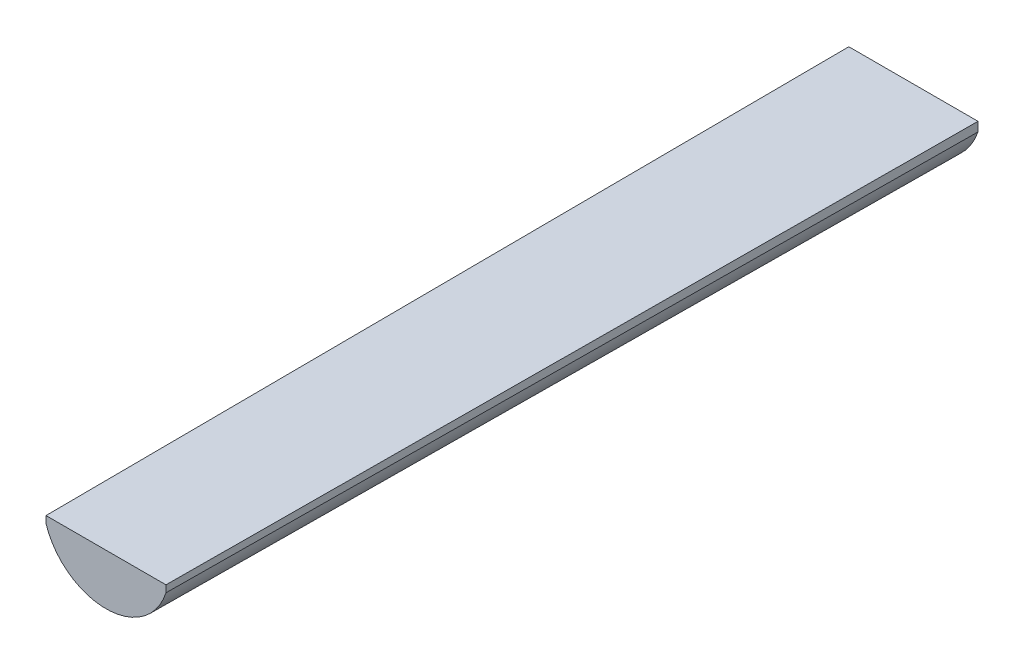
SolidWorks part; units mm, degrees
ref_plane "Přední rovina" through (0, 0, 0) normal (0, 0, 1) x (1, 0, 0)
ref_plane "Horní rovina" through (0, 0, 0) normal (0, 1, 0) x (1, 0, 0)
ref_plane "Pravá rovina" through (0, 0, 0) normal (1, 0, 0) x (0, 0, -1)
sketch "Skica1" plane through (0, 0, 0) normal (1, 0, 0) x (0, 0, -1)
  line L0 (0, 0) -> (350, 0)
  dimension "D1" = 350
sketch "Skica2" plane through (0, 0, 0) normal (0, 0, 1) x (1, 0, 0)
  line L0 (-26, 0) -> (26, 0)
  line L1 (26, 0) -> (26, -3)
  line L2 (-26, 0) -> (-26, -3)
  arc A0 (-26, -3) -> (26, -3) centre (0, 5.2895) ccw
  dimension "D1" = 52
  dimension "D2" = 22
  dimension "D3" = 3
ref_plane "Rovina1" through (0, 0, -350) normal (0, 0, 1) x (1, 0, 0)
sketch "Skica3" plane through (0, 0, -350) normal (0, 0, 1) x (1, 0, 0)
  line L0 (28, 0) -> (-28, 0)
  line L1 (-28, 0) -> (-28, -4)
  line L2 (28, 0) -> (28, -4)
  arc A0 (28, -4) -> (-28, -4) centre (0, 5.6) cw
  dimension "D1" = 56
  dimension "D2" = 4
  dimension "D3" = 24
loft "Spojit profily1" add profiles "Skica2", "Skica3"
sketch "Skica5" plane through (0, 0, 0) normal (0, 1, 0) x (1, 0, 0)
  line L0 (28, 350) -> (-28, 350)
  line L1 (28, 350) -> (27.9429, 340)
  line L2 (26, 0) -> (28, 350) construction
  line L3 (-28, 350) -> (-27.9429, 340)
  line L4 (-26, 0) -> (-28, 350) construction
  arc A0 (27.9429, 340) -> (-27.9429, 340) centre (0, 350.9177) cw
  dimension "D1" = 10
  dimension "D2" = 30
ref_plane "Rovina3" through (0, -100, 0) normal (0, 1, 0) x (1, 0, 0)
sketch "Skica6" plane through (0, -100, 0) normal (0, 1, 0) x (1, 0, 0)
  line L0 (-18, 350) -> (18, 350)
  line L1 (28, 350) -> (-28, 350) construction
  line L2 (-18, 350) -> (-18, 343)
  line L3 (18, 350) -> (18, 343)
  arc A0 (-18, 343) -> (18, 343) centre (0, 343) ccw
  point P2 (0, 350)
  dimension "D3" = 18
  dimension "D1" = 36
  dimension "D2" = 7
ref_plane "Rovina4" through (0, -175, -175) normal (0, -0.7071, -0.7071) x (-1, 0, 0)
sketch "Skica7" plane through (0, -175, -175) normal (0, -0.7071, -0.7071) x (-1, 0, 0)
  line L0 (28, 247.4874) -> (27.7657, 218.4883)
  line L1 (-28, 247.4874) -> (-27.7879, 218.4881)
  line L2 (28, 247.4874) -> (27.9429, 240.4163) construction
  line L3 (-26, -2.1213) -> (-28, 244.6589) construction
  line L4 (-28, 247.4874) -> (28, 247.4874)
  arc A0 (27.7657, 218.4883) -> (-27.7879, 218.4881) centre (-0.0111, 222.0168) cw
  dimension "D1" = 29
  dimension "D2" = 28
ref_plane "Rovina5" through (0, 0, -255) normal (0, 0, -1) x (-1, 0, 0)
sketch "Skica8" plane through (0, 0, -255) normal (0, 0, -1) x (-1, 0, 0)
  line L0 (-27.4571, 0) -> (-27.4571, -0.5)
  line L2 (27.4571, 0) -> (27.4571, -0.5)
  line L4 (-27.4571, 0) -> (27.4571, 0)
  arc A0 (-27.4571, -0.5) -> (27.4571, -0.5) centre (0, 4.9868) ccw
  dimension "D2" = 28
  dimension "D1" = 0.5
sketch3d "3DSkica1"
  line L0 (0.003, -23.0132, -255) -> (0, -24, -350) construction
  arc A0 (27.4571, -0.5, -255) -> (-27.4571, -0.5, -255) centre (0, 4.9868, -255) ccw construction
  arc A1 (-27.7657, -20.5054, -329.4946) -> (27.7879, -20.5055, -329.4945) centre (0.0111, -18.0104, -331.9896) ccw construction
  arc A2 (-18, -100, -343) -> (18, -100, -343) centre (0, -100, -343) ccw construction
  arc A3 (-28, -4, -350) -> (28, -4, -350) centre (0, 5.6, -350) ccw construction
  spline S0 degree 3 poles (0.003, -23.0132, -255) (0.0013, -23.5824, -309.8006) (0.8466, -39.5102, -332.8148) (0, -100, -325) knots 0 0 0 0 1 1 1 1
  point P9 (0, 4.9868, -283)
  point P13 (0.0111, 1.7886, -312.1906)
  point P17 (0, -82, -343)
  point P19 (0, 5.6, -320.4)
sketch3d "3DSkica3"
  line L0 (28, 0, -350) -> (28, -4, -350)
  line L1 (28, -4, -350) -> (18, -100, -350)
  line L2 (-28, 0, -350) -> (-27.4571, 0, -255)
  line L3 (28, 0, -350) -> (27.4571, 0, -255)
  line L4 (-18, -100, -350) -> (-28, -4, -350)
  line L5 (-28, -4, -350) -> (-28, 0, -350)
